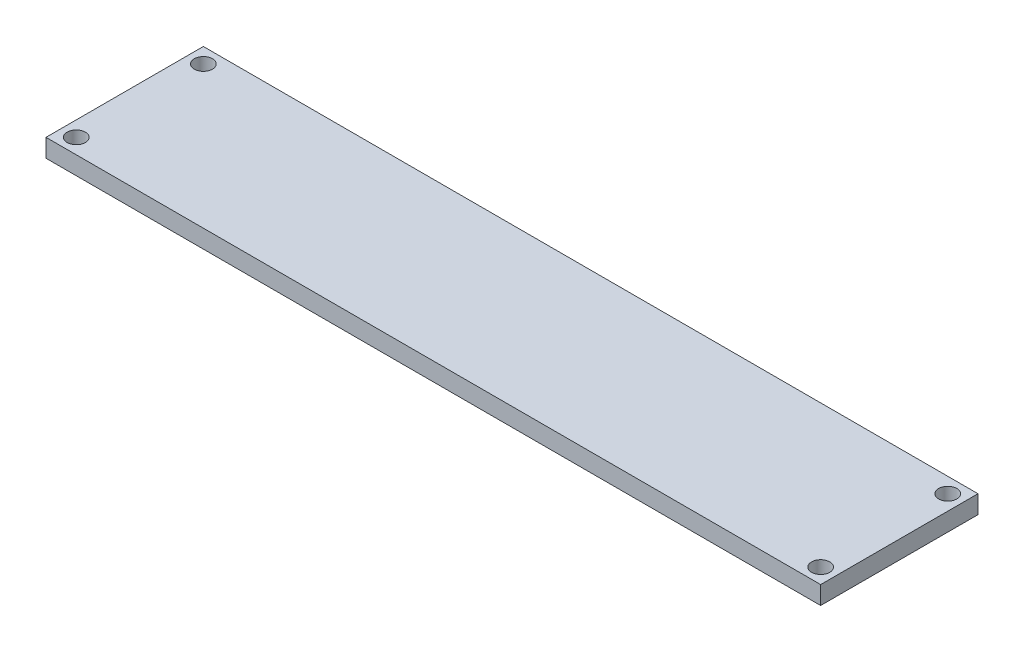
SolidWorks part; units mm, degrees
ref_plane "Front Plane" through (0, 0, 0) normal (0, 0, 1) x (1, 0, 0)
ref_plane "Top Plane" through (0, 0, 0) normal (0, 1, 0) x (1, 0, 0)
ref_plane "Right Plane" through (0, 0, 0) normal (1, 0, 0) x (0, 0, -1)
sketch "Sketch1" plane through (0, 0, 0) normal (0, 1, 0) x (1, 0, 0)
  line L1 (-64, -13) -> (64, -13)
  line L2 (-64, -13) -> (-64, 13)
  line L3 (-64, 13) -> (64, 13)
  line L4 (64, -13) -> (64, 13)
  line L5 (-64, -13) -> (64, 13) construction
  line L6 (-64, 13) -> (64, -13) construction
  circle A0 centre (-61.5, 10.5) radius 1.5
  circle A1 centre (61.5, 10.5) radius 1.5
  circle A2 centre (61.5, -10.5) radius 1.5
  circle A3 centre (-61.5, -10.5) radius 1.5
  point P0 (0, 0)
  dimension "D3" = 3
  dimension "D1" = 26
  dimension "D2" = 128
  dimension "D4" = 2.5
  dimension "D5" = 2.5
  dimension "D8" = 2.5
  dimension "D9" = 2.5
  dimension "D10" = 123
  dimension "D6" = 2
  dimension "D7" = 2
extrude "Boss-Extrude1" add sketch "Sketch1" against normal blind 3
